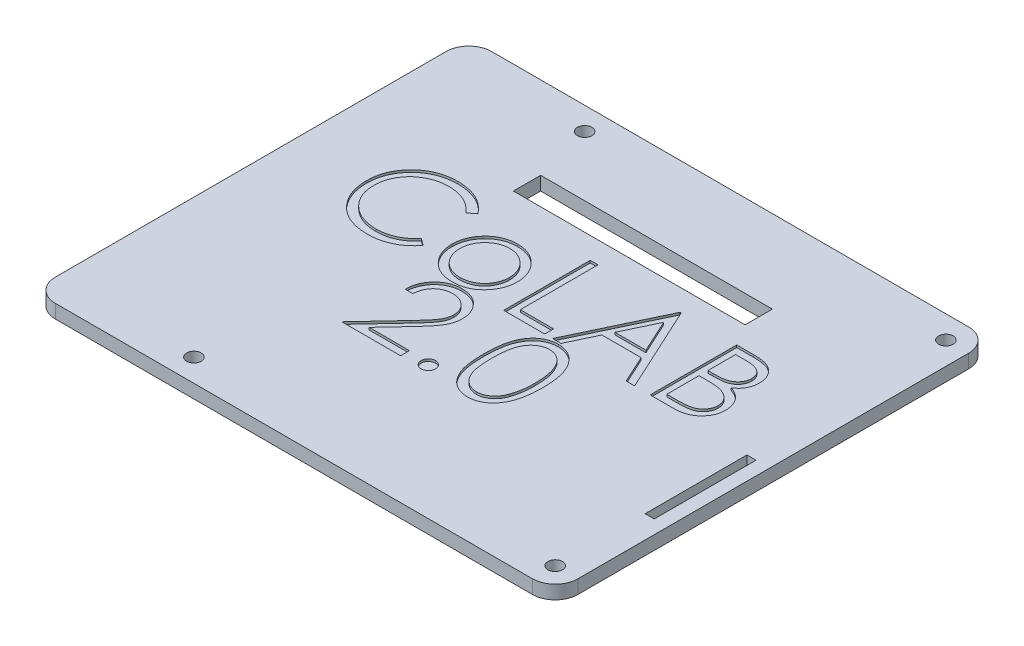
SolidWorks part; units mm, degrees
ref_plane "Front" through (0, 0, 0) normal (0, 0, 1) x (1, 0, 0)
ref_plane "Top" through (0, 0, 0) normal (0, 1, 0) x (1, 0, 0)
ref_plane "Right" through (0, 0, 0) normal (1, 0, 0) x (0, 0, -1)
sketch "Sketch1" plane through (0, 0, 0) normal (0, 1, 0) x (1, 0, 0)
  line L1 (5, 0) -> (110, 0)
  line L2 (0, 5) -> (0, 91)
  line L3 (5, 96) -> (110, 96)
  line L4 (115, 5) -> (115, 91)
  arc A0 (5, 0) -> (0, 5) centre (5, 5) cw
  arc A1 (110, 0) -> (115, 5) centre (110, 5) ccw
  arc A2 (110, 96) -> (115, 91) centre (110, 91) cw
  arc A3 (0, 91) -> (5, 96) centre (5, 91) cw
  point P7 (0, 0)
  point P10 (115, 0)
  point P15 (0, 96)
  dimension "D3" = 5
  dimension "D1" = 96
  dimension "D2" = 115
extrude "Boss-Extrude1" add sketch "Sketch1" along normal blind 3
sketch "Sketch2" plane through (0, 3, 0) normal (0, 1, 0) x (1, 0, 0)
  line L0 (0, 48) -> (115, 48) construction
  line L1 (0, 91) -> (0, 5) construction
  line L2 (115, 5) -> (115, 91) construction
  line L3 (0, 28) -> (115, 28) construction
  text T0 "CoLAB" font "Century Gothic" height in points 72
  text T1 "2.0" font "Century Gothic" height in points 72
  dimension "D1" = 20
extrude "Cut-Extrude1" cut sketch "Sketch2" against normal blind 0.5
sketch "Sketch3" plane through (0, 0, 0) normal (0, -1, 0) x (1, 0, 0)
  line L0 (0, -91) -> (0, -5) construction
  line L1 (110, -96) -> (5, -96) construction
  line L2 (0, -48) -> (115, -48) construction
  line L3 (115, -5) -> (115, -91) construction
  circle A0 centre (30.5, -91) radius 1.6
  circle A1 centre (110, -91) radius 1.6
  arc A2 (110, -96) -> (115, -91) centre (110, -91) ccw construction
  circle A3 centre (110, -5) radius 1.6
  circle A4 centre (30.5, -5) radius 1.6
  dimension "D1" = 30.5
  dimension "D3" = 3.2
  dimension "D2" = 5
extrude "Cut-Extrude2" cut sketch "Sketch3" against normal through all both and the other way through all
sketch "Sketch5" plane through (0, 3, 0) normal (0, 1, 0) x (1, 0, 0)
  line L0 (115, 5) -> (115, 91) construction
  line L1 (115, 47.2) -> (112, 47.2)
  line L2 (115, 47.2) -> (115, 24.8)
  line L3 (115, 24.8) -> (112, 24.8)
  line L4 (112, 47.2) -> (112, 24.8)
  line L5 (5, 0) -> (110, 0) construction
  line L7 (112, 47.2) -> (110, 47.2)
  line L8 (112, 47.2) -> (112, 24.8)
  line L9 (112, 24.8) -> (110, 24.8)
  line L10 (110, 47.2) -> (110, 24.8)
  dimension "D1" = 22.4
  dimension "D2" = 24.8
  dimension "D3" = 3
  dimension "D4" = 2
extrude "Cut-Extrude3" cut sketch "Sketch5" against normal through all both and the other way through all contours L7 L10 L9 L4
sketch "Sketch6" plane through (0, 0, 0) normal (0, -1, 0) x (1, 0, 0)
  line L0 (110, -96) -> (5, -96) construction
  line L1 (115, -5) -> (115, -91) construction
  circle A0 centre (92, -60) radius 1.45
  circle A1 centre (80, -23) radius 1.45
  circle A2 centre (55, -58.7) radius 1.45
  circle A3 centre (31.14, -20.6) radius 1.45
  circle A4 centre (12.34, -37.36) radius 1.45
  circle A5 centre (80, -23) radius 3.5
  circle A6 centre (92, -60) radius 3.5
  circle A7 centre (55, -58.7) radius 3.5
  circle A8 centre (12.34, -37.36) radius 3.5
  circle A9 centre (31.14, -20.6) radius 3.5
  dimension "D1" = 2.9
  dimension "D12" = 7
  dimension "D13" = 7
  dimension "D14" = 7
  dimension "D15" = 7
  dimension "D16" = 7
  dimension "D2" = 36
  dimension "D3" = 23
  dimension "D4" = 37
  dimension "D5" = 35
  dimension "D6" = 25
  dimension "D7" = 23.86
  dimension "D8" = 38.1
  dimension "D9" = 16.76
  dimension "D10" = 18.8
  dimension "D11" = 1.3
extrude "Boss-Extrude2" add sketch "Sketch6" along normal blind 5 contours A8 A4 | A9 A3 | A5 A1 | A7 A2 | A6 A0
sketch "Sketch7" plane through (0, 3, 0) normal (0, 1, 0) x (1, 0, 0)
  line L0 (115, 5) -> (115, 91) construction
  line L1 (34, 77.8) -> (85, 77.8)
  line L2 (34, 77.8) -> (34, 71.8)
  line L3 (34, 71.8) -> (85, 71.8)
  line L4 (85, 77.8) -> (85, 71.8)
  line L5 (0, 91) -> (0, 5) construction
  line L6 (110, 96) -> (5, 96) construction
  dimension "D1" = 30
  dimension "D2" = 34
  dimension "D3" = 18.2
  dimension "D4" = 6
extrude "Cut-Extrude4" cut sketch "Sketch7" against normal through all both and the other way through all
